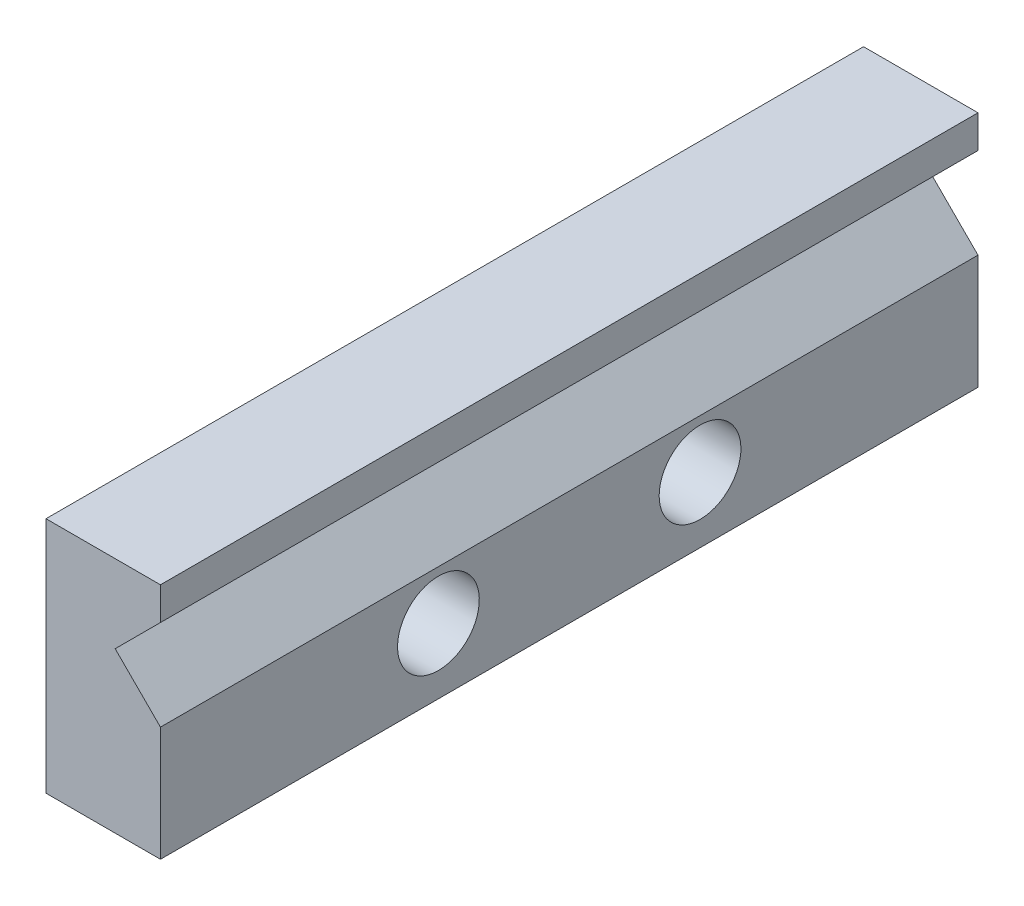
SolidWorks part; units mm, degrees
ref_plane "Front Plane" through (0, 0, 0) normal (0, 0, 1) x (1, 0, 0)
ref_plane "Top Plane" through (0, 0, 0) normal (0, 1, 0) x (1, 0, 0)
ref_plane "Right Plane" through (0, 0, 0) normal (1, 0, 0) x (0, 0, -1)
sketch "Sketch2" plane through (0, 0, 0) normal (0, 0, 1) x (1, 0, 0)
  line L0 (-52.0364, 78.4753) -> (-6.3368, 78.4753) construction
  line L1 (-15.7135, 63.6371) -> (-18.4835, 60.8671)
  line L2 (-18.4835, 60.8671) -> (-15.7135, 58.0971)
  line L3 (-15.7135, 58.0971) -> (-15.7135, 51.0971)
  line L4 (-15.7135, 51.0971) -> (-22.7135, 51.0971)
  line L5 (-22.7135, 51.0971) -> (-22.7135, 65.6371)
  line L6 (-22.7135, 65.6371) -> (-15.7135, 65.6371)
  line L7 (-15.7135, 65.6371) -> (-15.7135, 63.6371)
  dimension "D1" = 7
  dimension "D2" = 2
  dimension "D3" = 2.77
  dimension "D4" = 90
  dimension "D5" = 2.77
  dimension "D6" = 5.54
  dimension "D7" = 7
extrude "Boss-Extrude1" add sketch "Sketch2" along normal blind 50
sketch "Sketch3" plane through (-22.7135, 0, 0) normal (-1, 0, 0) x (0, 0, 1)
  line L2 (50, 51.0971) -> (0, 51.0971) construction
  line L3 (50, 65.6371) -> (50, 51.0971) construction
  line L4 (0, 65.6371) -> (0, 51.0971) construction
  circle A0 centre (17, 55.0971) radius 2.5
  circle A1 centre (33, 55.0971) radius 2.5
  dimension "D1" = 4
  dimension "D2" = 5
  dimension "D3" = 4
  dimension "D4" = 17
  dimension "D5" = 17
extrude "Cut-Extrude1" cut sketch "Sketch3" against normal up to next
